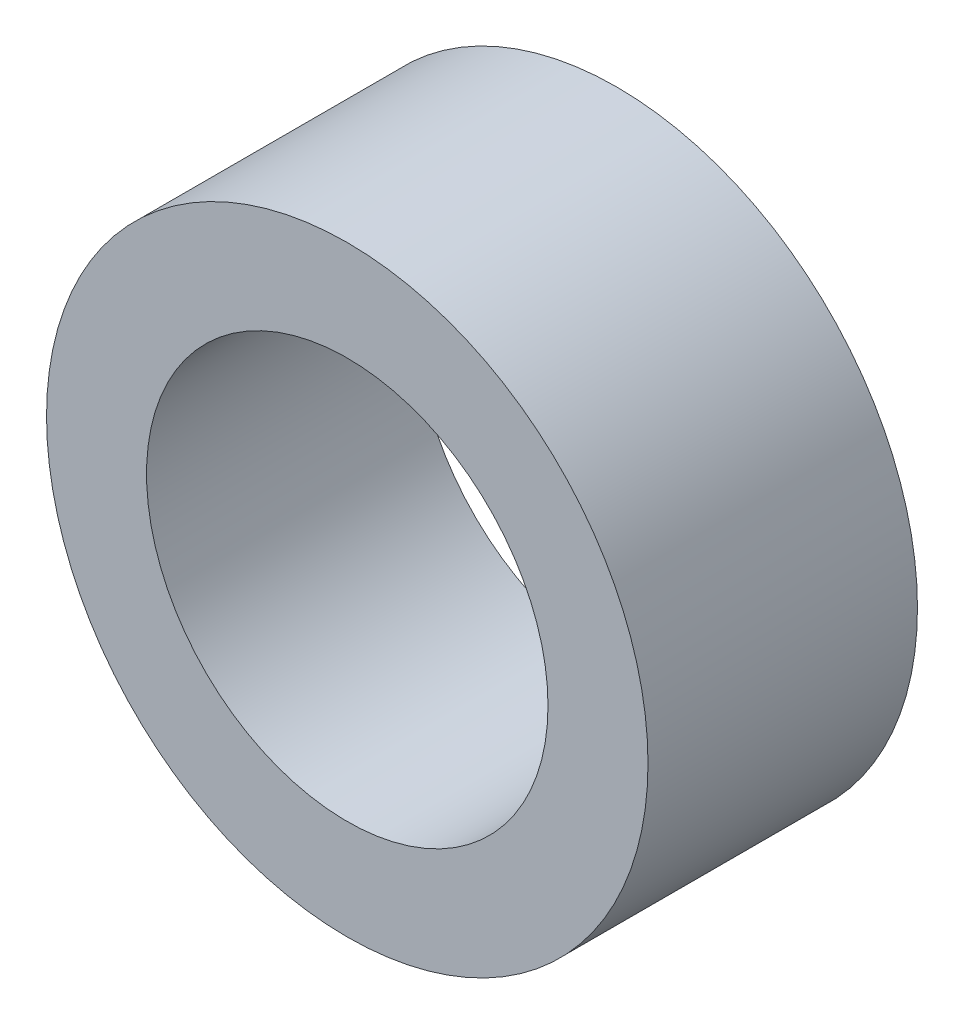
SolidWorks part; units mm, degrees
ref_plane "Front Plane" through (0, 0, 0) normal (0, 0, 1) x (1, 0, 0)
ref_plane "Top Plane" through (0, 0, 0) normal (0, 1, 0) x (1, 0, 0)
ref_plane "Right Plane" through (0, 0, 0) normal (1, 0, 0) x (0, 0, -1)
sketch "Sketch1" plane through (0, 0, 0) normal (0, 0, 1) x (1, 0, 0)
  circle A0 centre (0, 0) radius 4.7625
  circle A1 centre (0, 0) radius 3.1788
  point P4 (0, 4.7625)
  dimension "OD" = 9.525
  dimension "ID" = 6.3576
sketch "Sketch2" plane through (0, 0, 0) normal (1, 0, 0) x (0, 0, -1)
  line L0 (2.1336, 0) -> (-2.1336, 0) construction
  line L1 (2.1336, 4.7625) -> (-2.1336, 4.7625) construction
  point P4 (0, 0)
  point P9 (0, 4.7625)
  dimension "Length" = 4.2672
sketch "Sketch3" plane through (0, 0, 0) normal (0, 0, 1) x (1, 0, 0)
  circle A0 centre (0, 0) radius 4.7625 construction
  circle A1 centre (0, 0) radius 3.1788 construction
  circle A2 centre (0, 0) radius 4.7625
  circle A3 centre (0, 0) radius 3.1788
extrude "Boss-Extrude1" add sketch "Sketch3" against normal up to vertex (2.1336 mm away) and the other way up to vertex (2.1336 mm away) up to point (0, 0, -2.1336) other way up to point (0, 0, 2.1336)
